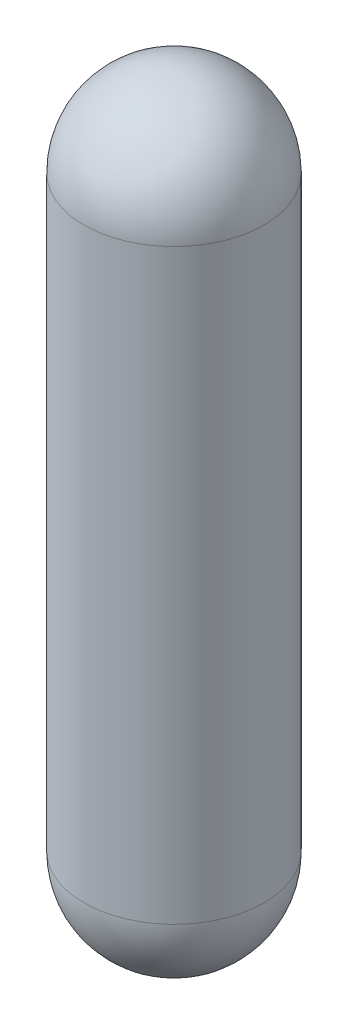
SolidWorks part; units mm, degrees
ref_plane "Front Plane" through (0, 0, 0) normal (0, 0, 1) x (1, 0, 0)
ref_plane "Top Plane" through (0, 0, 0) normal (0, 1, 0) x (1, 0, 0)
ref_plane "Right Plane" through (0, 0, 0) normal (1, 0, 0) x (0, 0, -1)
sketch "Sketch1" plane through (0, 0, 0) normal (0, 0, 1) x (1, 0, 0)
  line L5 (0, 8.27) -> (0, -8.77)
  line L6 (2, 6.27) -> (2, -6.77)
  arc A2 (2, 6.27) -> (0, 8.27) centre (0, 6.27) ccw
  arc A3 (0, -8.77) -> (2, -6.77) centre (0, -6.77) ccw
  point P3 (0, 0)
  dimension "D2" = 4
  dimension "D3" = 4
  dimension "D1" = 13.04
revolve "Revolve1" add sketch "Sketch1" angle 360 about L5
